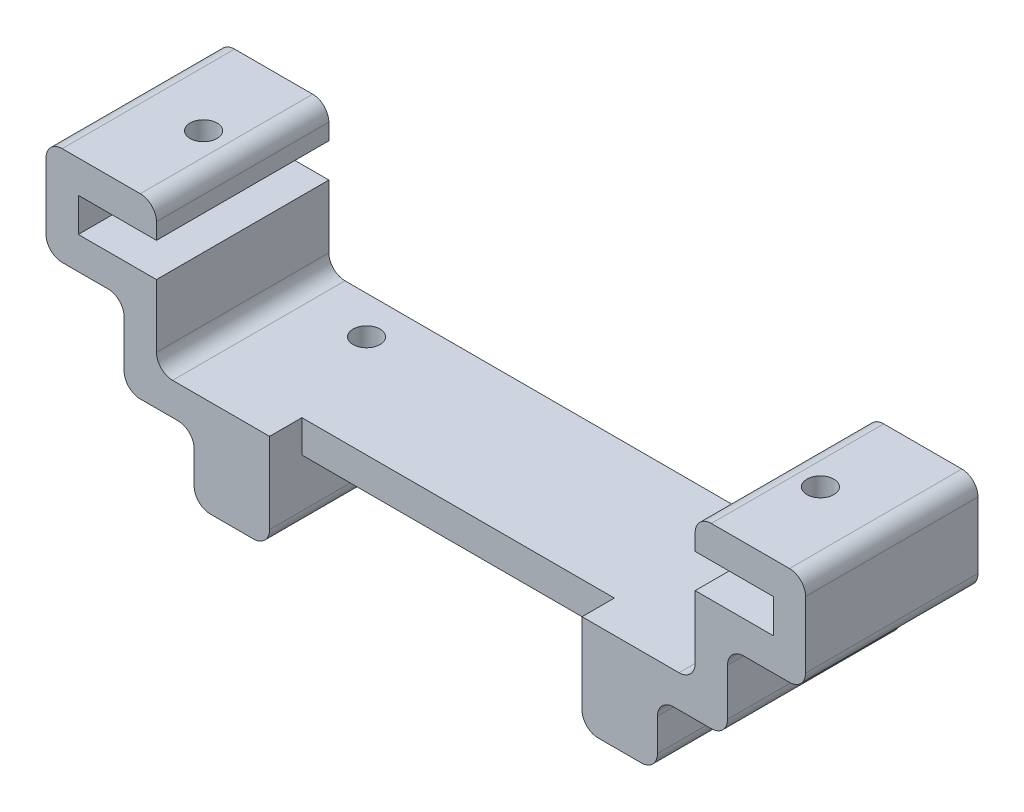
SolidWorks part; units mm, degrees
ref_plane "Front Plane" through (0, 0, 0) normal (0, 0, 1) x (1, 0, 0)
ref_plane "Top Plane" through (0, 0, 0) normal (0, 1, 0) x (1, 0, 0)
ref_plane "Right Plane" through (0, 0, 0) normal (1, 0, 0) x (0, 0, -1)
sketch "Sketch1" plane through (0, 0, 0) normal (0, 0, 1) x (1, 0, 0)
  line L0 (-32.25, 0) -> (-32.25, -3.15)
  line L1 (-32.25, -3.15) -> (-25, -3.15)
  line L2 (-35.25, -6.15) -> (-28, -6.15)
  line L3 (-25, -3.15) -> (-25, -10.5)
  line L4 (-25, -10.5) -> (25, -10.5)
  line L5 (25, -10.5) -> (25, -3.15)
  line L6 (-28, -6.15) -> (-28, -13.5)
  line L7 (25, -3.15) -> (32.25, -3.15)
  line L8 (32.25, -3.15) -> (32.25, 0)
  line L9 (32.25, 0) -> (25, 0)
  line L10 (28, -13.5) -> (28, -6.15)
  line L11 (25, 0) -> (25, 3)
  line L12 (25, 3) -> (35.25, 3)
  line L13 (35.25, 3) -> (35.25, -6.15)
  line L14 (21.5, -19.5) -> (14.5, -19.5)
  line L15 (-35.25, -6.15) -> (-35.25, 3)
  line L16 (-35.25, 3) -> (-25, 3)
  line L17 (-25, 3) -> (-25, 0)
  line L18 (-25, 0) -> (-32.25, 0)
  line L19 (28, -6.15) -> (35.25, -6.15)
  line L20 (-14.5, -19.5) -> (-14.5, -13.5)
  line L21 (-14.5, -13.5) -> (14.5, -13.5)
  line L22 (14.5, -13.5) -> (14.5, -19.5)
  line L23 (-28, -13.5) -> (-21.5, -13.5)
  line L24 (-21.5, -13.5) -> (-21.5, -19.5)
  line L25 (21.5, -19.5) -> (21.5, -13.5)
  line L26 (21.5, -13.5) -> (28, -13.5)
  line L27 (-14.5, -19.5) -> (-21.5, -19.5)
  point P2 (0, -10.5)
  point P6 (-18, -19.5)
  point P7 (18, -19.5)
  dimension "D1" = 3
  dimension "D2" = 3
  dimension "D3" = 50
  dimension "D4" = 22.5
  dimension "D5" = 3
  dimension "D6" = 64.5
  dimension "D7" = 3.15
  dimension "D9" = 3
  dimension "D10" = 3
  dimension "D11" = 29
  dimension "D12" = 36
  dimension "D13" = 6
extrude "Boss-Extrude1" add sketch "Sketch1" along normal blind 16
sketch "Sketch2" plane through (0, -10.5, 0) normal (0, 1, 0) x (1, 0, 0)
  line L0 (25, 0) -> (-25, 0) construction
  line L7 (25, -16) -> (-25, -16) construction
  line L8 (-18, -3.5) -> (18, -3.5) construction
  circle A0 centre (-18, -3.5) radius 1.25
  circle A1 centre (18, -3.5) radius 1.25
  point P10 (0, -16)
  point P14 (0, -3.5)
  dimension "D3" = 2.5
  dimension "D4" = 3.5
  dimension "D5" = 36
extrude "Cut-Extrude1" cut sketch "Sketch2" against normal through all
sketch "Sketch4" plane through (0, 3, 0) normal (0, 1, 0) x (1, 0, 0)
  line L1 (-25, -16) -> (-25, 0) construction
  line L2 (28.625, -8) -> (-28.625, -8) construction
  line L4 (-25, -16) -> (-32.25, -16) construction
  circle A0 centre (-28.625, -8) radius 1.25
  circle A1 centre (28.625, -8) radius 1.25
  point P7 (-25, -8)
  point P11 (0, -8)
  point P18 (-28.625, -16)
  dimension "D1" = 2.5
extrude "Cut-Extrude2" cut sketch "Sketch4" against normal up to next
fillet "Fillet1" radius 1.5 18 edges at (25, -10.5, 8) (-25, -10.5, 8) (35.25, 3, 8) (-35.25, 3, 8) (-25, 3, 8) (25, 3, 8) (35.25, -6.15, 8) (28, -6.15, 8) (-28, -6.15, 8) (-35.25, -6.15, 8) (-21.5, -19.5, 8) (-14.5, -19.5, 8) (21.5, -19.5, 8) (14.5, -19.5, 8) (28, -13.5, 8) (21.5, -13.5, 8) (-21.5, -13.5, 8) (-28, -13.5, 8)
sketch "Sketch8" plane through (0, -10.5, 0) normal (0, 1, 0) x (1, 0, 0)
  line L0 (23.5, -16) -> (-23.5, -16) construction
  line L1 (-14.5, -16) -> (14.5, -16)
  line L2 (-14.5, -16) -> (-14.5, -13)
  line L3 (-14.5, -13) -> (14.5, -13)
  line L4 (14.5, -16) -> (14.5, -13)
  line L5 (-14.5, -16) -> (14.5, -13) construction
  line L6 (-14.5, -13) -> (14.5, -16) construction
  point P4 (0, -14.5)
  dimension "D1" = 3
  dimension "D2" = 29
extrude "Cut-Extrude3" cut sketch "Sketch8" against normal through all
